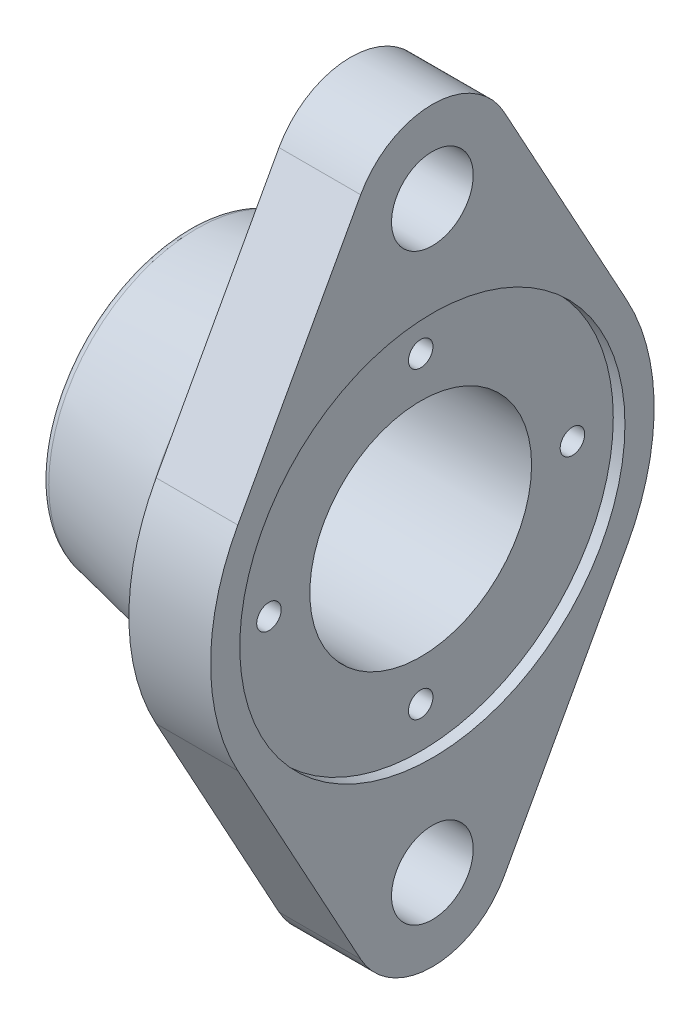
SolidWorks part; units mm, degrees
material "42 2420"
ref_plane "Přední rovina" through (0, 0, 0) normal (0, 0, 1) x (1, 0, 0)
ref_plane "Vrchní rovina" through (0, 0, 0) normal (0, 1, 0) x (1, 0, 0)
ref_plane "Pravá rovina" through (0, 0, 0) normal (1, 0, 0) x (0, 0, -1)
sketch "Skica1" plane through (0, 0, 0) normal (0, 0, 1) x (1, 0, 0)
  line L0 (0, 19) -> (0, 32.5)
  line L5 (0, 32.5) -> (-4, 32.5)
  line L6 (-4, 32.5) -> (-4, 30)
  line L7 (-4, 30) -> (-28, 25)
  line L8 (-28, 25) -> (-28, 22.5)
  line L9 (-28, 22.5) -> (-24, 22.5)
  line L10 (-24, 22.5) -> (-24, 19)
  line L11 (-24, 19) -> (0, 19)
  line L13 (-37.4302, 0) -> (5.7841, 0) construction
  dimension "D1" = 65
  dimension "D2" = 60
  dimension "D3" = 50
  dimension "D4" = 38
  dimension "D5" = 45
  dimension "D6" = 28
  dimension "D7" = 4
  dimension "D8" = 4
revolve "Rotovat1" add sketch "Skica1" angle 360 about L13
sketch "Skica2" plane through (0, 0, 0) normal (1, 0, 0) x (0, 0, -1)
  line L0 (-33.3362, -18.24) -> (-12.2818, -56.72)
  line L1 (12.2818, -56.72) -> (33.3362, -18.24)
  line L2 (33.3362, 18.24) -> (12.2818, 56.72)
  line L3 (-12.2818, 56.72) -> (-33.3362, 18.24)
  line L4 (-86.7174, 0) -> (115.2804, 0) construction
  line L5 (0, 121.61) -> (0, -128.1909) construction
  circle A0 centre (0, 0) radius 19 construction
  circle A1 centre (0, 0) radius 19
  arc A2 (-12.2818, -56.72) -> (12.2818, -56.72) centre (0, -50) ccw
  arc A3 (33.3362, -18.24) -> (33.3362, 18.24) centre (0, 0) ccw
  arc A4 (12.2818, 56.72) -> (-12.2818, 56.72) centre (0, 50) ccw
  arc A5 (-33.3362, 18.24) -> (-33.3362, -18.24) centre (0, 0) ccw
  circle A6 centre (0, 50) radius 7
  circle A7 centre (0, -50) radius 7
  dimension "D1" = 50
  dimension "D3" = 14
  dimension "D4" = 38
  dimension "D5" = 14
  dimension "D2" = 50
extrude "Přidat vysunutím1" add sketch "Skica2" along normal blind 14
fillet "Zaoblit1" radius 3 1 edges at (-4, 0, 30)
sketch "Skica3" plane through (14, 0, 0) normal (1, 0, 0) x (0, 0, -1)
  circle A0 centre (0, 0) radius 19 construction
  circle A1 centre (0, 0) radius 19
  circle A2 centre (0, 0) radius 33
  dimension "D1" = 66
extrude "Odebrat vysunutím1" cut sketch "Skica3" against normal blind 2
chamfer "Zkosení1" distance 2 angle 45 1 edges at (-24, 0, 19)
fillet "Zaoblit2" radius 2 2 edges at (0, 0, 32.5) (-28, 0, 25)
hole_wizard "M5 závit1" positions "Skica4" profile "Skica6" tap size "M5" standard "ISO"
sketch "Skica4" plane through (12, 0, 0) normal (1, 0, 0) x (0, 0, -1)
  line L0 (-44.0788, 0) -> (50.2573, 0) construction
  line L2 (0, 33.3793) -> (0, -35.3384) construction
  point P10 (-26, 0)
  dimension "D1" = 26
sketch "Skica6" plane through (12, 0, 26) normal (0, 1, 0) x (0, 0, -1)
  line L0 (0, 0) -> (0, 11.2618)
  line L1 (0, 11.2618) -> (2.1, 10)
  line L2 (2.1, 10) -> (2.1, 0)
  line L5 (2.1, 0) -> (0, 0)
  line L10 (0, 11.2618) -> (-2.1, 10) construction
  line L11 (0, -6.35) -> (0, 107.95) construction
  dimension "Průměr závitníku" = 4.2
  dimension "Hloubka závitníku" = 10
  dimension "Úhel vrtání" = 118
cosmetic thread "Závit díry1" parameters "D1"=8, "D2"=5
pattern_circular "Kruhové pole1" count 4 over 360 about axis through (0, 0, 0) along (1, 0, 0) of "M5 závit1"
